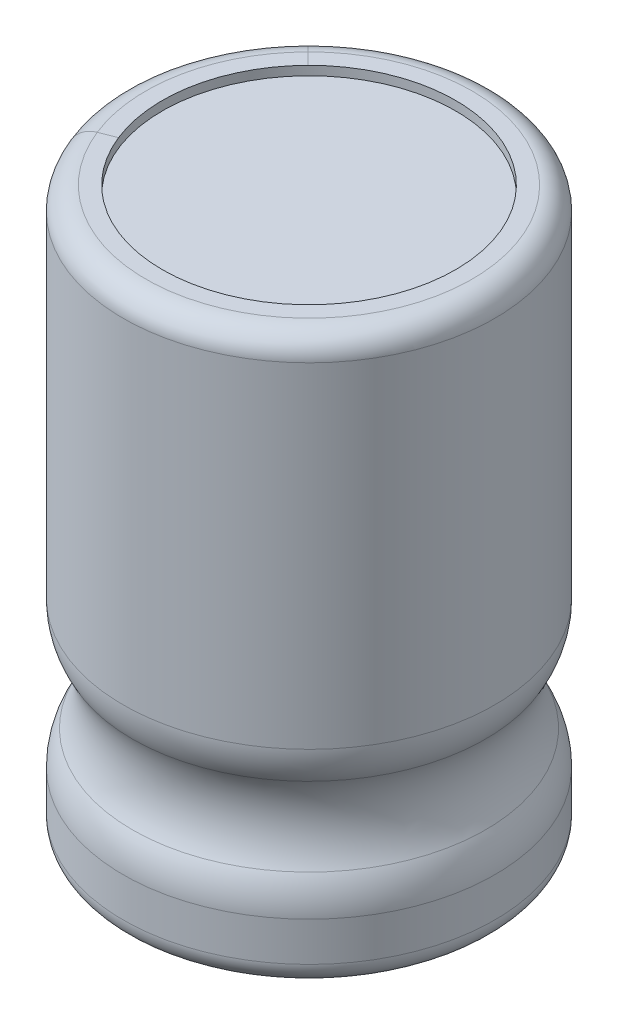
SolidWorks part; units mm, degrees
ref_plane "Alzado" through (0, 0, 0) normal (0, 0, 1) x (1, 0, 0)
ref_plane "Planta" through (0, 0, 0) normal (0, 1, 0) x (1, 0, 0)
ref_plane "Vista lateral" through (0, 0, 0) normal (1, 0, 0) x (0, 0, -1)
sketch "Croquis1" plane through (0, 0, 0) normal (0, 1, 0) x (1, 0, 0)
  circle A0 centre (0, 0) radius 4.1
  dimension "D1" = 8.2
extrude "Extruir1" add sketch "Croquis1" along normal blind 12.5
sketch "Croquis2" plane through (0, 0, 0) normal (1, 0, 0) x (0, 0, -1)
  line L1 (0, 12.5) -> (0, 14.4205) construction
  line L2 (4.1, 12.5) -> (-4.1, 12.5) construction
  circle A0 centre (5.382, 2.9878) radius 1.7211
revolve "Cortar-Revolución1" cut sketch "Croquis2" angle 360 about L1
fillet "Redondeo1" radius 0.5 2 edges at (0, 0, 4.1) (0, 12.5, 4.1)
fillet "Redondeo2" radius 1.5 2 edges at (0, 4.1361, -4.1) (0, 1.8395, 4.1)
sketch "Croquis3" plane through (0, 12.5, 0) normal (0, 1, 0) x (1, 0, 0)
  circle A0 centre (0, 0) radius 3.237
extrude "Cortar-Extruir1" cut sketch "Croquis3" against normal blind 0.2
ref_plane "Plano1" through (0, 14, 0) normal (0, 1, 0) x (-1, 0, 0)
sketch "Croquis4" plane through (0, 14, 0) normal (0, 1, 0) x (-1, 0, 0)
  line L0 (0, 0) -> (5.9595, 2.3678)
  line L1 (5.9595, 2.3678) -> (5.9595, -5.9004)
  line L2 (5.9595, -5.9004) -> (0, 0)
split line "Línea de partición1"
